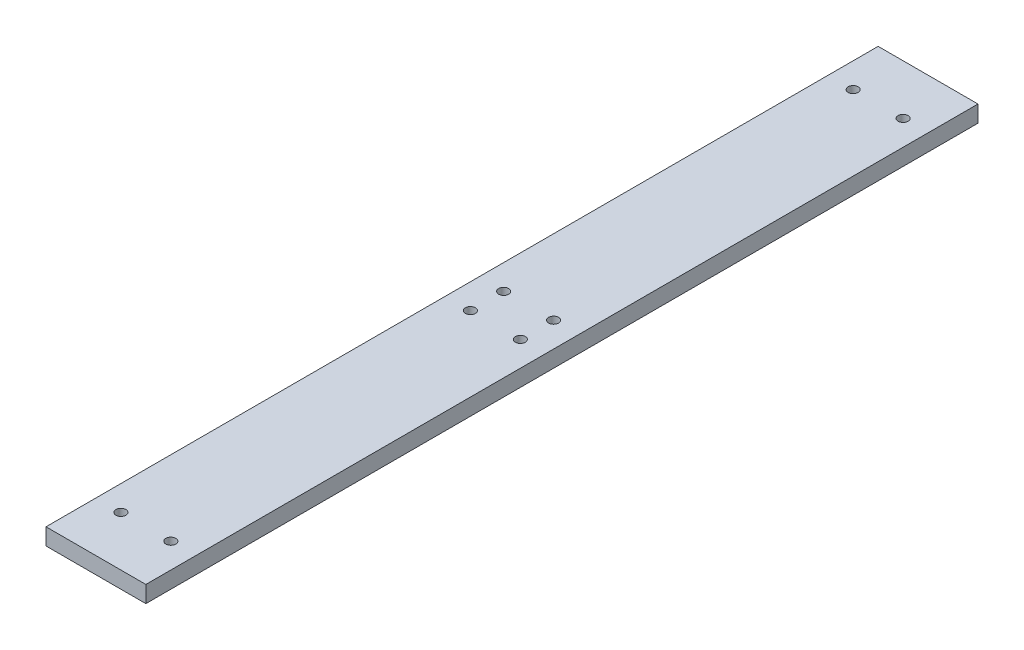
SolidWorks part; units mm, degrees
ref_plane "Спереди" through (0, 0, 0) normal (0, 0, 1) x (1, 0, 0)
ref_plane "Сверху" through (0, 0, 0) normal (0, 1, 0) x (1, 0, 0)
ref_plane "Справа" through (0, 0, 0) normal (1, 0, 0) x (0, 0, -1)
sketch "Эскиз1" plane through (0, 0, 0) normal (0, 1, 0) x (1, 0, 0)
  line L0 (-105.9673, 500) -> (120, 500) construction
  line L1 (0, 0) -> (120, 0)
  line L2 (0, 0) -> (0, 1000)
  line L3 (0, 1000) -> (120, 1000)
  line L4 (120, 0) -> (120, 1000)
  line L5 (60, 0) -> (60, 1038.2254) construction
  line L6 (-25.7708, 270) -> (240.3622, 270) construction
  circle A1 centre (30, 60) radius 6
  circle A2 centre (90, 60) radius 6
  circle A3 centre (90, 480) radius 6
  circle A4 centre (30, 480) radius 6
  circle A5 centre (90, 520) radius 6
  circle A6 centre (90, 940) radius 6
  circle A7 centre (30, 940) radius 6
  circle A8 centre (30, 520) radius 6
extrude "Бобышка-Вытянуть1" add sketch "Эскиз1" along normal blind 20
